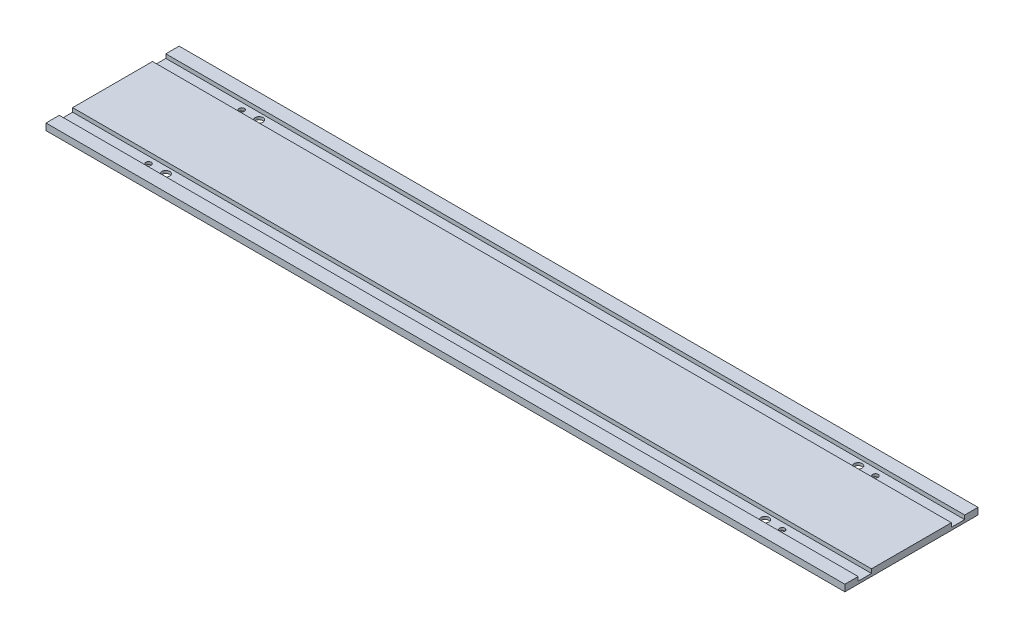
SolidWorks part; units mm, degrees
ref_plane "Front Plane" through (0, 0, 0) normal (0, 0, 1) x (1, 0, 0)
ref_plane "Top Plane" through (0, 0, 0) normal (0, 1, 0) x (1, 0, 0)
ref_plane "Right Plane" through (0, 0, 0) normal (1, 0, 0) x (0, 0, -1)
sketch "Sketch1" plane through (0, 0, 0) normal (0, 0, 1) x (1, 0, 0)
  line L0 (0, 0) -> (600, 0)
  line L1 (600, 0) -> (600, 5)
  line L2 (600, 5) -> (0, 5)
  line L3 (0, 5) -> (0, 0)
  dimension "D1" = 600
  dimension "D2" = 5
extrude "Boss-Extrude1" add sketch "Sketch1" against normal blind 100
sketch "Sketch5" plane through (0, 5, 0) normal (0, 1, 0) x (1, 0, 0)
  line L2 (0, 90) -> (600, 90)
  line L6 (0, 80) -> (600, 80)
  line L8 (0, 90) -> (0, 80)
  line L9 (600, 90) -> (600, 80)
  line L10 (0, 20) -> (0, 10)
  line L11 (600, 20) -> (600, 10)
  line L12 (0, 20) -> (600, 20)
  line L13 (0, 10) -> (600, 10)
extrude "Cut-Extrude1" cut sketch "Sketch5" against normal blind 3
sketch "Sketch6" plane through (0, 5, 0) normal (0, 1, 0) x (1, 0, 0)
  circle A0 centre (62, 85) radius 2
  circle A1 centre (62, 15) radius 2
  circle A2 centre (538, 85) radius 2
  circle A3 centre (538, 15) radius 2
extrude "Cut-Extrude2" cut sketch "Sketch6" against normal through all
sketch "Sketch7" plane through (0, 5, 0) normal (0, 1, 0) x (1, 0, 0)
  circle A0 centre (75, 85) radius 3
  circle A1 centre (75, 15) radius 3
  circle A2 centre (525, 85) radius 3
  circle A3 centre (525, 15) radius 3
extrude "Cut-Extrude3" cut sketch "Sketch7" against normal through all
